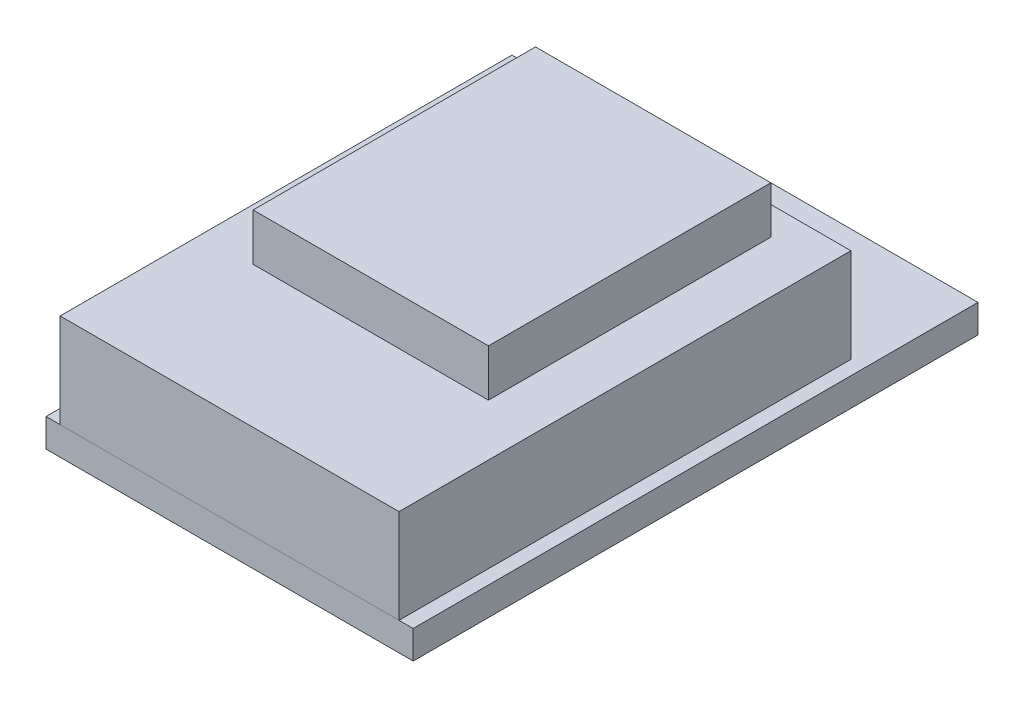
SolidWorks part; units mm, degrees
ref_plane "Спереди" through (0, 0, 0) normal (0, 0, 1) x (1, 0, 0)
ref_plane "Сверху" through (0, 0, 0) normal (0, 1, 0) x (1, 0, 0)
ref_plane "Справа" through (0, 0, 0) normal (1, 0, 0) x (0, 0, -1)
sketch "Эскиз1" plane through (0, 0, 0) normal (0, 1, 0) x (1, 0, 0)
  line L1 (-9.75, -15) -> (9.75, -15)
  line L2 (-9.75, -15) -> (-9.75, 15)
  line L3 (-9.75, 15) -> (9.75, 15)
  line L4 (9.75, -15) -> (9.75, 15)
  line L5 (-9.75, -15) -> (9.75, 15) construction
  line L6 (-9.75, 15) -> (9.75, -15) construction
  point P0 (0, 0)
  dimension "D1" = 30
  dimension "D2" = 19.5
extrude "Бобышка-Вытянуть1" add sketch "Эскиз1" along normal blind 1.5
sketch "Эскиз2" plane through (0, 0, 0) normal (0, -1, 0) x (1, 0, 0)
  line L0 (0, 15) -> (0, -15) construction
  line L1 (-9.75, 15) -> (9.75, 15) construction
  line L2 (9.75, -15) -> (-9.75, -15) construction
  line L3 (-3.81, 11.19) -> (-3.81, -9.13) construction
  line L4 (-5.08, 11.19) -> (-2.54, 11.19)
  line L5 (-5.08, 11.19) -> (-5.08, -9.13)
  line L6 (-5.08, -9.13) -> (-2.54, -9.13)
  line L7 (-2.54, 11.19) -> (-2.54, -9.13)
  line L8 (3.81, 11.19) -> (3.81, -9.13) construction
  line L9 (2.54, 11.19) -> (2.54, -9.13)
  line L10 (5.08, -9.13) -> (2.54, -9.13)
  line L11 (5.08, 11.19) -> (5.08, -9.13)
  line L12 (5.08, 11.19) -> (2.54, 11.19)
  dimension "D1" = 2.54
  dimension "D2" = 20.32
  dimension "D3" = 3.81
  dimension "D4" = 3.81
extrude "Бобышка-Вытянуть2" add sketch "Эскиз2" along normal blind 2.54 separate body
sketch "Эскиз3" plane through (0, 1.5, 0) normal (0, 1, 0) x (1, 0, 0)
  line L0 (0, 15) -> (0, -15) construction
  line L1 (9.75, 15) -> (-9.75, 15) construction
  line L2 (-9.75, -15) -> (9.75, -15) construction
  line L4 (-9, 9) -> (9, 9)
  line L5 (-9, 9) -> (-9, -15)
  line L6 (-9, -15) -> (9, -15)
  line L7 (9, 9) -> (9, -15)
  line L8 (-9, 9) -> (9, -15) construction
  line L9 (-9, -15) -> (9, 9) construction
  point P6 (0, -3)
  dimension "D1" = 18
  dimension "D2" = 24
extrude "Бобышка-Вытянуть3" add sketch "Эскиз3" along normal blind 5 separate body
sketch "Эскиз4" plane through (0, 6.5, 0) normal (0, 1, 0) x (1, 0, 0)
  line L0 (0, 9) -> (0, -15) construction
  line L1 (9, 9) -> (-9, 9) construction
  line L2 (-9, -15) -> (9, -15) construction
  line L4 (6.25, -7.5) -> (-6.25, -7.5)
  line L5 (6.25, -7.5) -> (6.25, 7.5)
  line L6 (6.25, 7.5) -> (-6.25, 7.5)
  line L7 (-6.25, -7.5) -> (-6.25, 7.5)
  line L8 (6.25, -7.5) -> (-6.25, 7.5) construction
  line L9 (6.25, 7.5) -> (-6.25, -7.5) construction
  point P6 (0, 0)
  dimension "D1" = 12.5
  dimension "D2" = 15
  dimension "D3" = 1.5
extrude "Бобышка-Вытянуть4" add sketch "Эскиз4" along normal blind 2.5
